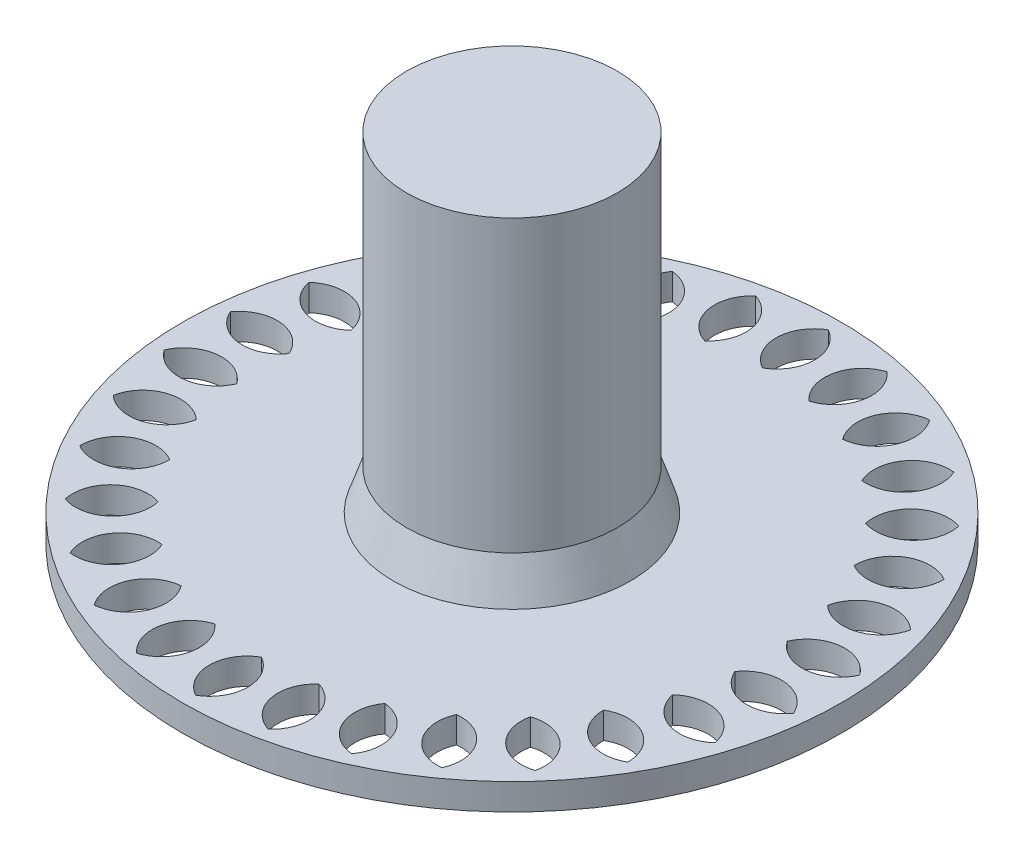
SolidWorks part; units mm, degrees
ref_plane "Front Plane" through (0, 0, 0) normal (0, 0, 1) x (1, 0, 0)
ref_plane "Top Plane" through (0, 0, 0) normal (0, 1, 0) x (1, 0, 0)
ref_plane "Right Plane" through (0, 0, 0) normal (1, 0, 0) x (0, 0, -1)
sketch "Sketch1" plane through (0, 0, 0) normal (0, 1, 0) x (1, 0, 0)
  line L0 (0, 24) -> (0, 19) construction
  arc A3 (0, 19) -> (0, 24) centre (1.4113, 21.5) cw
  arc A4 (0, 19) -> (0, 24) centre (-1.4113, 21.5) ccw
  dimension "D1" = 19
  dimension "D2" = 5
sketch "Sketch2" plane through (0, 0, 0) normal (0, 1, 0) x (1, 0, 0)
  circle A0 centre (0, 0) radius 25
  dimension "D1" = 50
extrude "Boss-Extrude1" add sketch "Sketch2" along normal blind 2
extrude "Cut-Extrude1" cut sketch "Sketch1" along normal through all
pattern_circular "CirPattern1" count 30 over 360 about axis through (0, 0, 0) along (0, 1, 0) of "Cut-Extrude1"
sketch "Sketch4" plane through (0, 0, 0) normal (0, 0, 1) x (1, 0, 0)
  line L1 (-8, 5) -> (0, 5)
  line L2 (0, 5) -> (0, 2)
  line L3 (25, 2) -> (-25, 2) construction
  line L5 (-9, 2) -> (0, 2)
  line L6 (-8, 5) -> (-9, 2)
  dimension "D1" = 3
  dimension "D2" = 8
  dimension "D3" = 9
revolve "Revolve1" add sketch "Sketch4" angle 360 about L2
sketch "Sketch5" plane through (0, 5, 0) normal (0, 1, 0) x (1, 0, 0)
  circle A0 centre (0, 0) radius 8
extrude "Boss-Extrude2" add sketch "Sketch5" along normal blind 22
